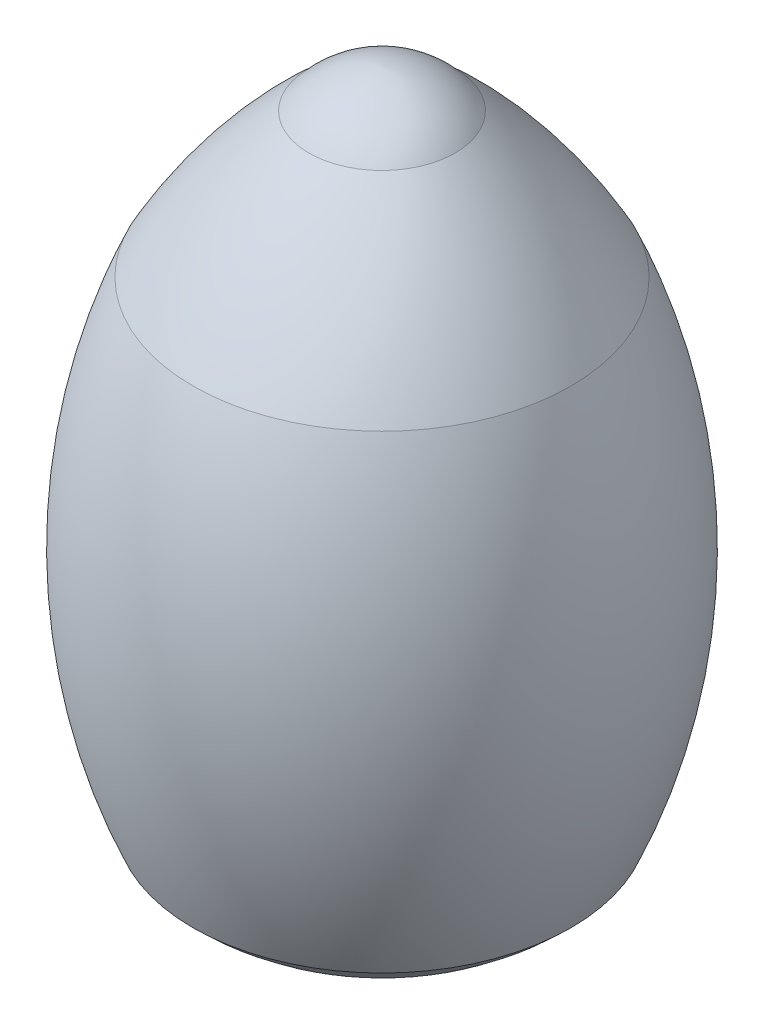
SolidWorks part; units mm, degrees
ref_plane "Front Plane" through (0, 0, 0) normal (0, 0, 1) x (1, 0, 0)
ref_plane "Top Plane" through (0, 0, 0) normal (0, 1, 0) x (1, 0, 0)
ref_plane "Right Plane" through (0, 0, 0) normal (1, 0, 0) x (0, 0, -1)
sketch "Sketch1" plane through (0, 0, 0) normal (0, 0, 1) x (1, 0, 0)
  line L0 (0, 0) -> (0, 500)
  line L1 (0, 0) -> (-130, 0) construction
  line L2 (-130, 0) -> (-130, 1053.6033) construction
  arc A0 (-130, 375.0466) -> (-130, 52.0527) centre (245.6028, 213.5497) ccw
  arc A1 (-50.3657, 474.1718) -> (0, 500) centre (5.0081, 428.2127) cw
  arc A2 (-82.6447, 18.9844) -> (0, 0) centre (36.2083, 347.0066) ccw
  arc A3 (-82.6447, 18.9844) -> (-130, 52.0527) centre (-14.4806, 167.0399) cw
  arc A4 (-130, 375.0466) -> (-50.3657, 474.1718) centre (198.9908, 192.2955) cw
  dimension "D1" = 500
  dimension "D2" = 130
revolve "Revolve1" add sketch "Sketch1" angle 360 about L0
